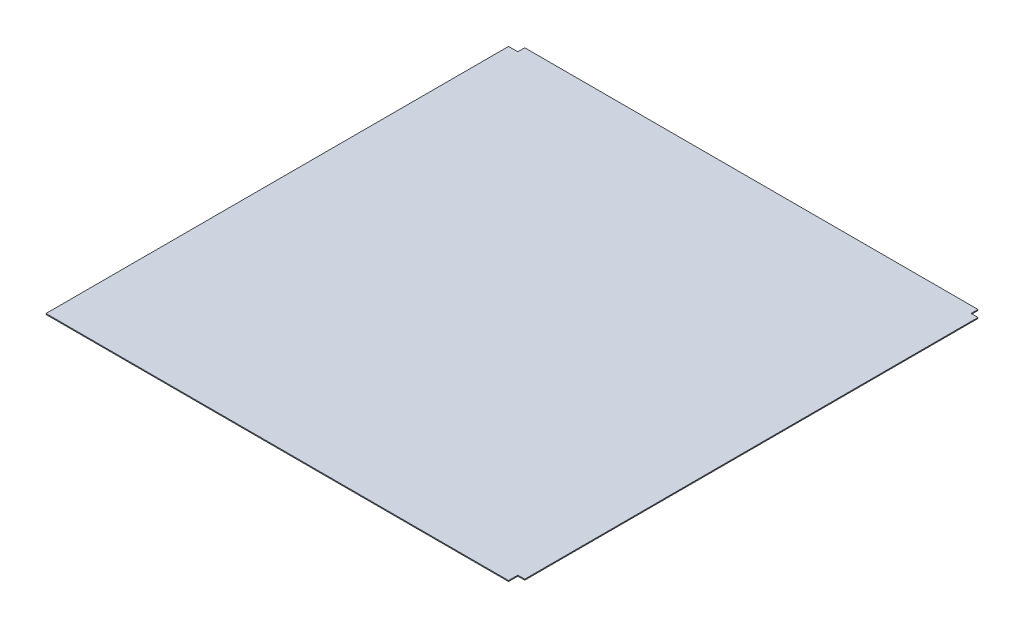
SolidWorks part; units mm, degrees
material "Aço galvanizado"
ref_plane "Plano frontal" through (0, 0, 0) normal (0, 0, 1) x (1, 0, 0)
ref_plane "Plano superior" through (0, 0, 0) normal (0, 1, 0) x (1, 0, 0)
ref_plane "Plano direito" through (0, 0, 0) normal (1, 0, 0) x (0, 0, -1)
sketch "Esboço1" plane through (0, 0, 0) normal (0, 1, 0) x (1, 0, 0)
  line L1 (-487.5, 507.5) -> (492.5, 507.5)
  line L2 (-507.5, 492.5) -> (-507.5, -507.5)
  line L3 (-507.5, -507.5) -> (492.5, -507.5)
  line L4 (507.5, 492.5) -> (507.5, -487.5)
  line L5 (-507.5, 507.5) -> (492.5, -492.5) construction
  line L6 (-507.5, -507.5) -> (507.5, 507.5) construction
  line L9 (507.5, 492.5) -> (492.5, 492.5)
  line L10 (492.5, 507.5) -> (492.5, 492.5)
  line L13 (-507.5, 492.5) -> (-487.5, 492.5)
  line L14 (-487.5, 507.5) -> (-487.5, 492.5)
  line L17 (507.5, -487.5) -> (492.5, -487.5)
  line L18 (492.5, -507.5) -> (492.5, -487.5)
  point P0 (0, 0)
  dimension "D1" = 1015
  dimension "D3" = 15
  dimension "D4" = 15
  dimension "D5" = 20
  dimension "D6" = 15
  dimension "D7" = 15
  dimension "D8" = 20
extrude "Ressalto-extrusão1" add sketch "Esboço1" along normal mid plane 2
